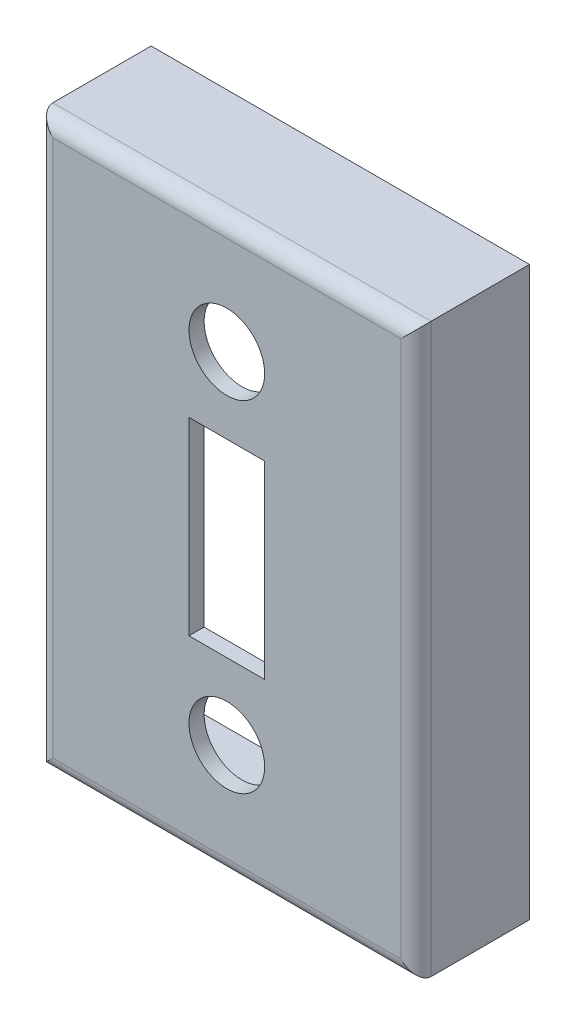
SolidWorks part; units mm, degrees
ref_plane "Front Plane" through (0, 0, 0) normal (0, 0, 1) x (1, 0, 0)
ref_plane "Top Plane" through (0, 0, 0) normal (0, 1, 0) x (1, 0, 0)
ref_plane "Right Plane" through (0, 0, 0) normal (1, 0, 0) x (0, 0, -1)
sketch "Sketch1" plane through (0, 0, 0) normal (0, 0, 1) x (1, 0, 0)
  line L1 (0, 0) -> (50, 0)
  line L2 (0, 0) -> (0, 75)
  line L3 (0, 75) -> (50, 75)
  line L4 (50, 0) -> (50, 75)
  dimension "D1" = 50
  dimension "D2" = 75
extrude "Boss-Extrude1" add sketch "Sketch1" along normal blind 15
shell "Shell3" thickness 2
fillet "Fillet1" radius 2 4 edges at (0, 37.5, 15) (25, 0, 15) (50, 37.5, 15) (25, 75, 15)
sketch "Sketch2" plane through (0, 0, 15) normal (0, 0, 1) x (1, 0, 0)
  line L0 (50, 75) -> (50, 0) construction
  line L1 (20, 50) -> (30, 50)
  line L2 (20, 50) -> (20, 25)
  line L3 (20, 25) -> (30, 25)
  line L4 (30, 50) -> (30, 25)
  line L6 (0, 75) -> (50, 75) construction
  line L8 (50, 0) -> (0, 0) construction
  circle A0 centre (25, 60) radius 5
  circle A1 centre (25, 15) radius 5
  dimension "D3" = 10
  dimension "D10" = 10
  dimension "D1" = 20
  dimension "D2" = 25
  dimension "D4" = 25
  dimension "D5" = 10
  dimension "D6" = 25
  dimension "D7" = 25
  dimension "D8" = 15
  dimension "D9" = 15
extrude "Cut-Extrude1" cut sketch "Sketch2" against normal through all
